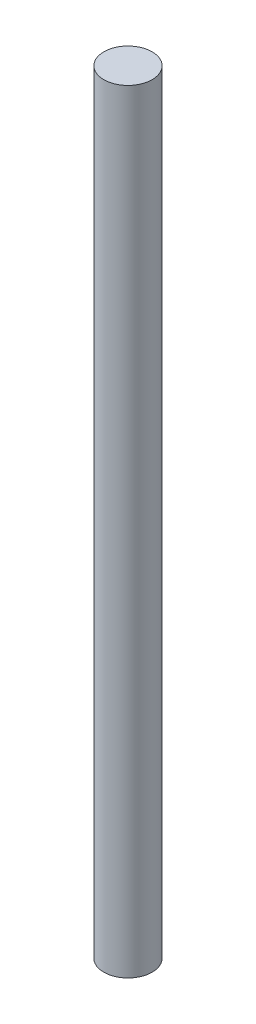
SolidWorks part; units mm, degrees
material "Brass"
ref_plane "Front Plane" through (0, 0, 0) normal (0, 0, 1) x (1, 0, 0)
ref_plane "Top Plane" through (0, 0, 0) normal (0, 1, 0) x (1, 0, 0)
ref_plane "Right Plane" through (0, 0, 0) normal (1, 0, 0) x (0, 0, -1)
sketch "Sketch2" plane through (0, 0, 0) normal (0, 1, 0) x (1, 0, 0)
  circle A0 centre (0, 0) radius 1.27
  dimension "D1" = 2.54
extrude "Boss-Extrude1" add sketch "Sketch2" along normal mid plane 40.64
